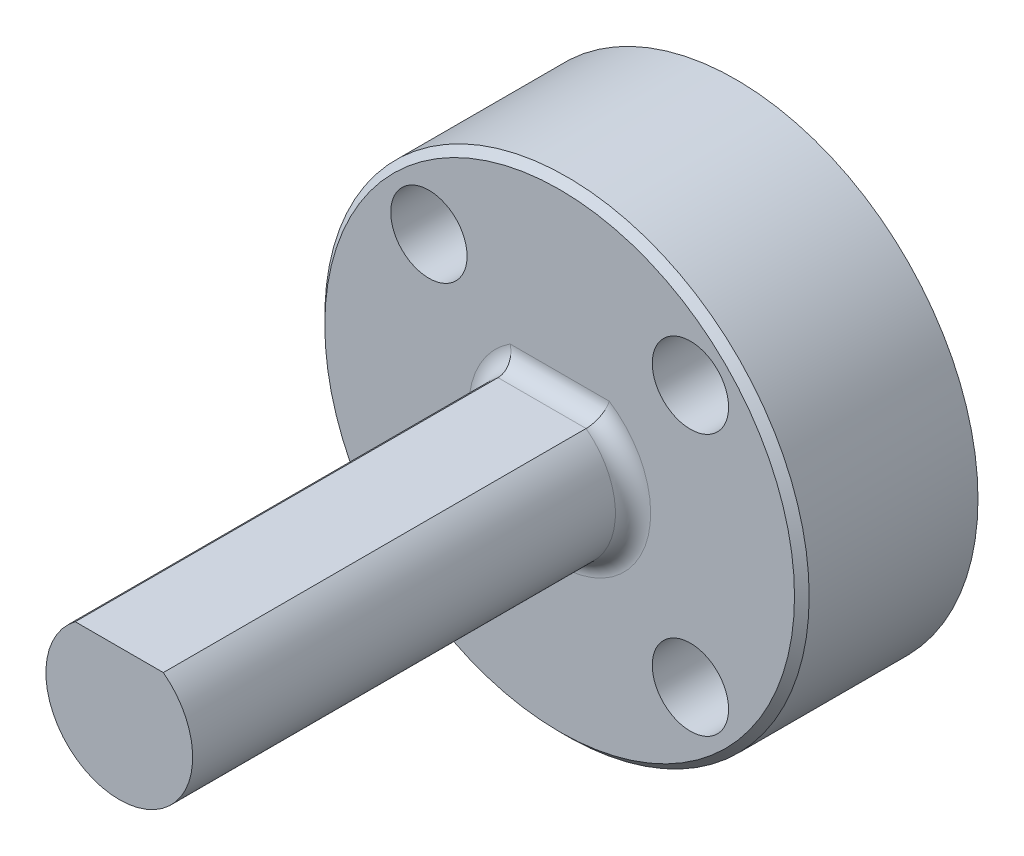
SolidWorks part; units mm, degrees
material "ABS"
ref_plane "Plan de face" through (0, 0, 0) normal (0, 0, 1) x (1, 0, 0)
ref_plane "Plan de dessus" through (0, 0, 0) normal (0, 1, 0) x (1, 0, 0)
ref_plane "Plan de droite" through (0, 0, 0) normal (1, 0, 0) x (0, 0, -1)
sketch "Esquisse1" plane through (0, 0, 0) normal (0, 0, 1) x (1, 0, 0)
  circle A0 centre (0, 12) radius 10.4775
  dimension "D1" = 20.955
extrude "Boss.-Extru.1" add sketch "Esquisse1" along normal blind 7.62
sketch "Esquisse3" plane through (0, 0, 0) normal (0, 0, -1) x (-1, 0, 0)
  circle A1 centre (0, 12) radius 4.1275
  dimension "D1" = 8.255
extrude "Enlèv. mat.-Extru.1" cut sketch "Esquisse3" against normal blind 2.286
sketch "Esquisse4" plane through (0, 0, 2.286) normal (0, 0, -1) x (-1, 0, 0)
  circle A1 centre (0, 12) radius 2.413
  dimension "D1" = 4.826
extrude "Enlèv. mat.-Extru.2" cut sketch "Esquisse4" against normal blind 2.286
sketch "Esquisse5" plane through (0, 0, 7.62) normal (0, 0, 1) x (1, 0, 0)
  line L1 (-1.905, 14.54) -> (1.905, 14.54)
  arc A1 (-1.905, 14.54) -> (1.905, 14.54) centre (0, 12) ccw
  dimension "D1" = 6.35
  dimension "D2" = 3.81
extrude "Boss.-Extru.2" add sketch "Esquisse5" along normal blind 19.05
sketch "Esquisse6" plane through (0, 0, 0) normal (0, 0, -1) x (-1, 0, 0)
  circle A0 centre (-5.6569, 17.6569) radius 1.27
  circle A1 centre (5.6569, 17.6569) radius 1.27
  circle A2 centre (5.6569, 6.3431) radius 1.27
  circle A3 centre (-5.6569, 6.3431) radius 1.27
  dimension "D1" = 2.54
extrude "Enlèv. mat.-Extru.3" cut sketch "Esquisse6" against normal through all both and the other way through all
sketch "Esquisse7" plane through (0, 0, 7.62) normal (0, 0, 1) x (1, 0, 0)
  circle A0 centre (-5.6569, 17.6569) radius 1.651
  circle A1 centre (5.6569, 17.6569) radius 1.651
  circle A2 centre (5.6569, 6.3431) radius 1.651
  circle A3 centre (-5.6569, 6.3431) radius 1.651
  dimension "D1" = 3.302
extrude "Enlèv. mat.-Extru.4" cut sketch "Esquisse7" against normal blind 4.318
chamfer "Chanfrein1" distance 0.3175 angle 45 1 edges at (10.4775, 12, 7.62)
fillet "Congé1" radius 0.762 2 edges at (0, 14.54, 7.62) (0, 8.825, 7.62)
